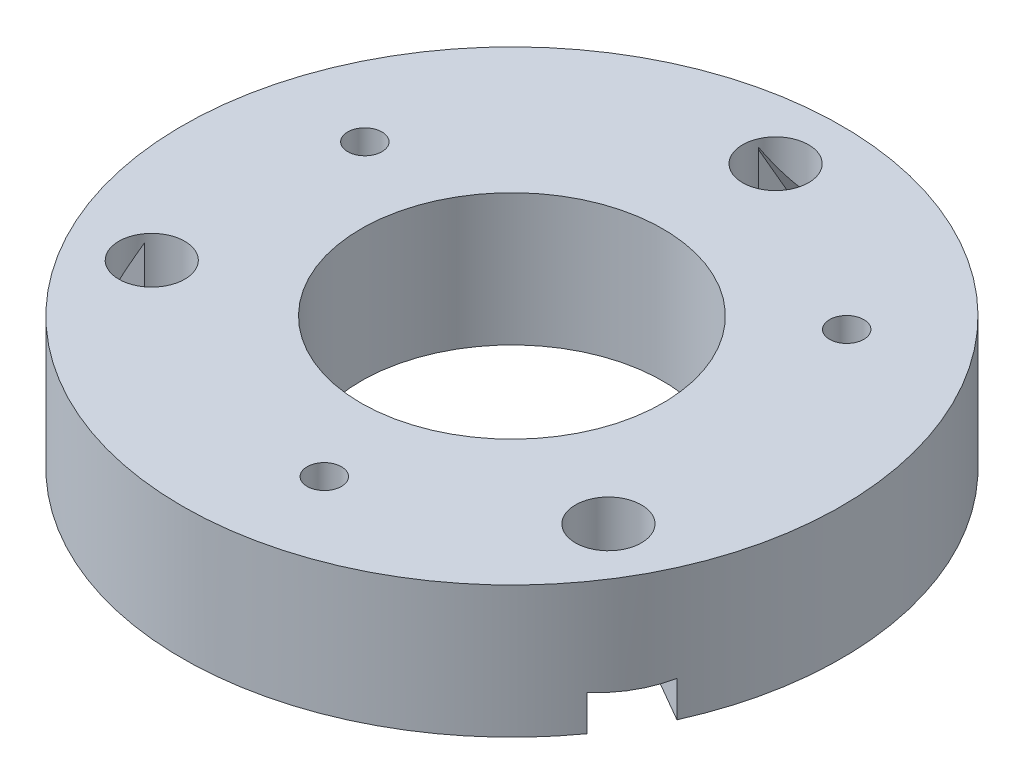
SolidWorks part; units mm, degrees
material "Custom Plastic"
ref_plane "Front Plane" through (0, 0, 0) normal (0, 0, 1) x (1, 0, 0)
ref_plane "Top Plane" through (0, 0, 0) normal (0, 1, 0) x (1, 0, 0)
ref_plane "Right Plane" through (0, 0, 0) normal (1, 0, 0) x (0, 0, -1)
sketch "Sketch1" plane through (0, 0, 0) normal (0, 1, 0) x (1, 0, 0)
  circle A0 centre (0, 0) radius 29.083
  circle A1 centre (0, 0) radius 63.5
  circle A2 centre (0, 50.8) radius 6.35
  circle A3 centre (43.9941, -25.4) radius 6.35
  circle A4 centre (-43.9941, -25.4) radius 6.35
  point P13 (0, 0)
  dimension "D1" = 58.166
  dimension "D2" = 127
  dimension "D3" = 12.7
  dimension "D4" = 50.8
  dimension "D5" = 3
extrude "Boss-Extrude1" add sketch "Sketch1" along normal blind 25.4
sketch "Sketch4" plane through (0, 0, 0) normal (1, 0, 0) x (0, 0, -1)
  line L0 (63.5, 0) -> (63.5, 6.35)
  line L1 (63.5, 6.35) -> (53.3603, 23.9124)
  line L2 (53.3603, 23.9124) -> (53.3603, 0)
  line L3 (53.3603, 0) -> (63.5, 0)
  line L4 (44.45, 0) -> (57.15, 0) construction
  line L7 (63.5, 6.35) -> (63.5, 15.4599) construction
  dimension "D1" = 30
  dimension "D2" = 6.35
extrude "Cut-Extrude3" cut sketch "Sketch4" against normal mid plane 12.7
pattern_circular "CirPattern1" count 3 over 360 about axis through (0, 0, 0) along (0, 1, 0) of "Cut-Extrude3"
sketch "Sketch5" plane through (0, 25.4, 0) normal (0, 1, 0) x (1, 0, 0)
  line L0 (0, 0) -> (-43.2291, 14.885) construction
  line L1 (0, 0) -> (0, 57.15) construction
  circle A0 centre (-43.2291, 14.885) radius 3.302
  circle A1 centre (0, 50.8) radius 6.35 construction
  dimension "D1" = 6.604
  dimension "D2" = 71
  dimension "D3" = 45.72
extrude "Cut-Extrude4" cut sketch "Sketch5" against normal through all
pattern_circular "CirPattern2" count 3 over 360 about axis through (0, 0, 0) along (0, 1, 0) of "Cut-Extrude4"
